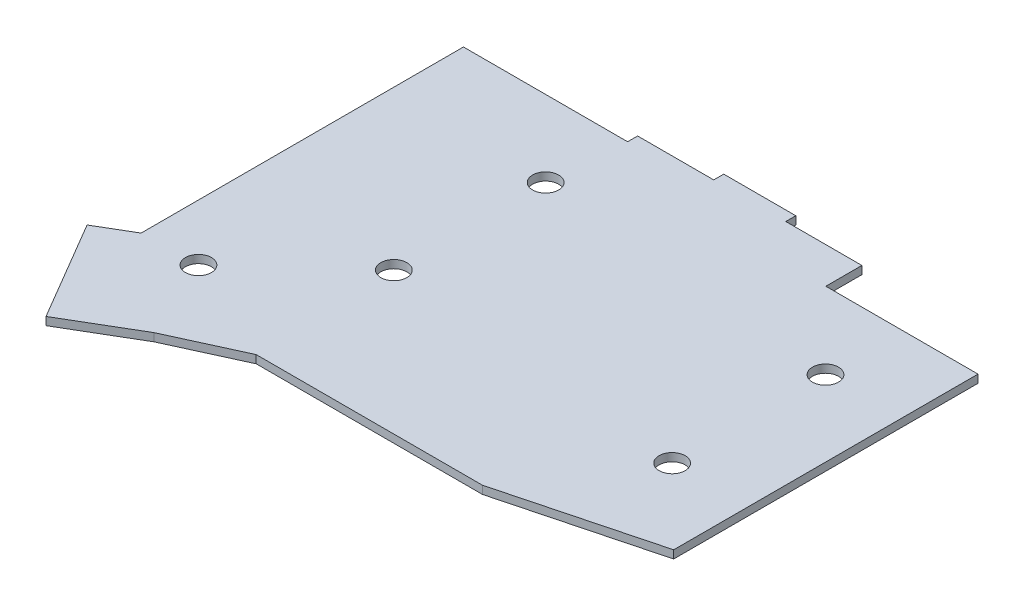
SolidWorks part; units mm, degrees
ref_plane "Спереди" through (0, 0, 0) normal (0, 0, 1) x (1, 0, 0)
ref_plane "Сверху" through (0, 0, 0) normal (0, 1, 0) x (1, 0, 0)
ref_plane "Справа" through (0, 0, 0) normal (1, 0, 0) x (0, 0, -1)
sketch "Эскиз1" plane through (0, 0, 0) normal (0, 1, 0) x (1, 0, 0)
  line L0 (0, 0) -> (0, -80.5)
  line L3 (41, 0) -> (0, 0)
  line L4 (41, 0) -> (41, 2.5)
  line L5 (41, 2.5) -> (60, 2.5)
  line L6 (60, 2.5) -> (60, 5)
  line L7 (60, 5) -> (78, 5)
  line L8 (78, 5) -> (78, 2.5)
  line L9 (78, 2.5) -> (97, 2.5)
  line L10 (97, 2.5) -> (97, -6.5)
  line L11 (97, -6.5) -> (135, -6.5)
  line L12 (135, -6.5) -> (135, -82.5)
  line L13 (135, -82.5) -> (97.1532, -92.4105)
  line L14 (97.1532, -92.4105) -> (40.6532, -92.4105)
  line L15 (0, 0) -> (0, -80.5) construction
  line L16 (0, -80.5) -> (-8.5, -85.5)
  line L17 (-8.5, -85.5) -> (6.1532, -110.4105)
  line L18 (6.1532, -110.4105) -> (23.1532, -100.4105)
  line L19 (23.1532, -100.4105) -> (40.6532, -92.4105)
  circle A2 centre (14.07, -80.258) radius 3.25
  circle A3 centre (39.57, -56.958) radius 3.25
  circle A4 centre (116.07, -63.958) radius 3.25
  circle A5 centre (116.07, -25.658) radius 3.25
  circle A6 centre (39.57, -19.048) radius 3.25
  dimension "D1" = 6.5
extrude "Бобышка-Вытянуть1" add sketch "Эскиз1" along normal blind 2
